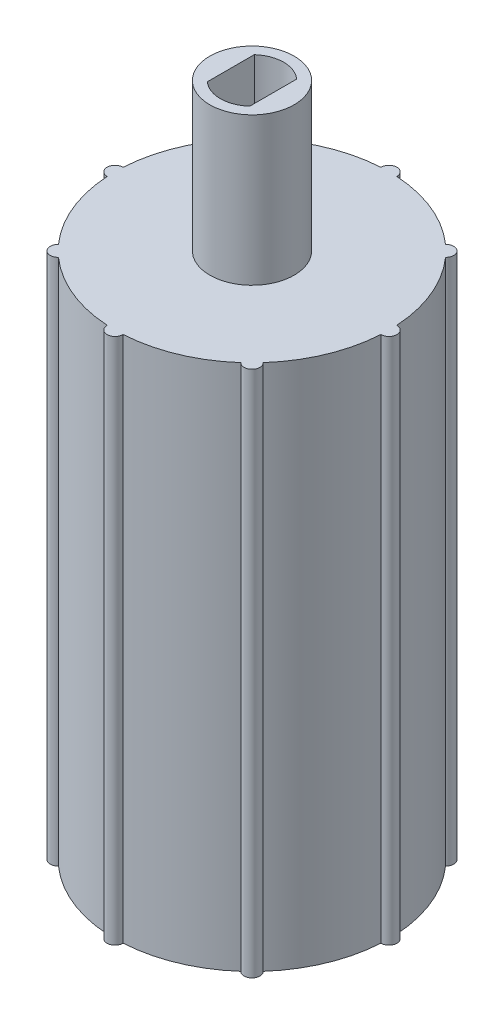
SolidWorks part; units mm, degrees
ref_plane "Plan de face" through (0, 0, 0) normal (0, 0, 1) x (1, 0, 0)
ref_plane "Plan de dessus" through (0, 0, 0) normal (0, 1, 0) x (1, 0, 0)
ref_plane "Plan de droite" through (0, 0, 0) normal (1, 0, 0) x (0, 0, -1)
sketch "Esquisse2" plane through (0, 0, 0) normal (0, 1, 0) x (1, 0, 0)
  circle A0 centre (0, 0) radius 13
  dimension "D1" = 26
extrude "Boss.-Extru.1" add sketch "Esquisse2" along normal blind 50
sketch "Esquisse3" plane through (0, 0, 0) normal (0, -1, 0) x (1, 0, 0)
  circle A0 centre (0, 0) radius 9
  dimension "D1" = 18
extrude "Enlèv. mat.-Extru.1" cut sketch "Esquisse3" against normal through all
sketch "Esquisse4" plane through (0, 0, 0) normal (0, -1, 0) x (1, 0, 0)
  circle A0 centre (0, 0) radius 11
  dimension "D1" = 22
extrude "Enlèv. mat.-Extru.2" cut sketch "Esquisse4" against normal blind 7
sketch "Esquisse6" plane through (0, 0, 0) normal (0, -1, 0) x (-1, 0, 0)
  circle A0 centre (-13, 0) radius 0.75
  circle A1 centre (0, 0) radius 13 construction
  dimension "D1" = 1.5
extrude "Boss.-Extru.2" add sketch "Esquisse6" against normal blind 50 contours A0
pattern_circular "Répétition circulaire1" count 8 over 360 about axis through (0, 0, 0) along (0, 1, 0) of "Boss.-Extru.2"
sketch "Esquisse7" plane through (0, 50, 0) normal (0, 1, 0) x (1, 0, 0)
  circle A0 centre (0, 0) radius 9
extrude "Boss.-Extru.3" add sketch "Esquisse7" against normal blind 3
sketch "Esquisse8" plane through (0, 50, 0) normal (0, 1, 0) x (1, 0, 0)
  circle A0 centre (0, 0) radius 4
  dimension "D1" = 8
extrude "Boss.-Extru.5" add sketch "Esquisse8" along normal blind 14
sketch "Esquisse10" plane through (0, 64, 0) normal (0, 1, 0) x (1, 0, 0)
  line L0 (-2.0099, -2.2272) -> (-2.0099, 2.2272)
  line L3 (2.0099, -2.2272) -> (2.0099, 2.2272)
  line L4 (-1.6698, -2.4924) -> (1.6698, 2.4924) construction
  line L5 (-1.6698, 2.4924) -> (1.6698, -2.4924) construction
  arc A0 (-2.0099, -2.2272) -> (2.0099, -2.2272) centre (0, 0) ccw
  arc A1 (2.0099, 2.2272) -> (-2.0099, 2.2272) centre (0, 0) ccw
  dimension "D1" = 6
extrude "Enlèv. mat.-Extru.4" cut sketch "Esquisse10" against normal blind 14
ref_plane "Plan1" through (0, 25, 0) normal (0, 1, 0) x (1, 0, 0)
sketch "Esquisse11" plane through (0, 25, 0) normal (0, 1, 0) x (1, 0, 0)
  circle A0 centre (0, 0) radius 13.755 construction
  dimension "D1" = 27.51
